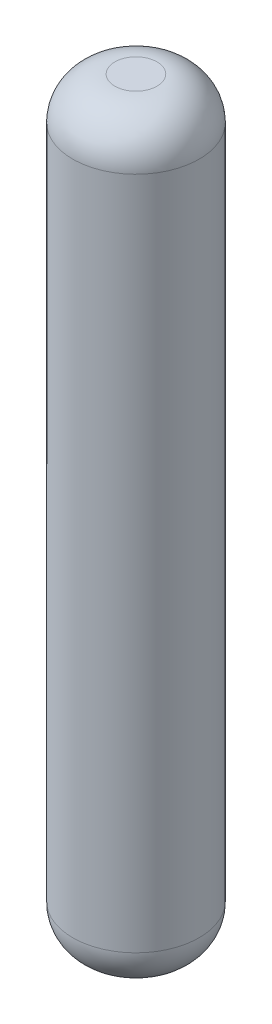
SolidWorks part; units mm, degrees
material "1.4000 (X6Cr13)"
ref_plane "Спереди" through (0, 0, 0) normal (0, 0, 1) x (1, 0, 0)
ref_plane "Сверху" through (0, 0, 0) normal (0, 1, 0) x (1, 0, 0)
ref_plane "Справа" through (0, 0, 0) normal (1, 0, 0) x (0, 0, -1)
sketch "Эскиз1" plane through (0, 0, 0) normal (0, 0, 1) x (1, 0, 0)
  line L0 (-2.0264, -0.1938) -> (-2.0264, -18.1938)
  line L1 (-1.5264, -0.1938) -> (-2.0264, -0.1938)
  line L2 (-1.5264, -18.1938) -> (-2.0264, -18.1938)
  line L4 (-0.5264, -1.1938) -> (-0.5264, -17.1938)
  arc A1 (-0.5264, -1.1938) -> (-1.5264, -0.1938) centre (-1.5264, -1.1938) ccw
  arc A2 (-1.5264, -18.1938) -> (-0.5264, -17.1938) centre (-1.5264, -17.1938) ccw
revolve "Повернуть3" add sketch "Эскиз1" angle 360 about L0
